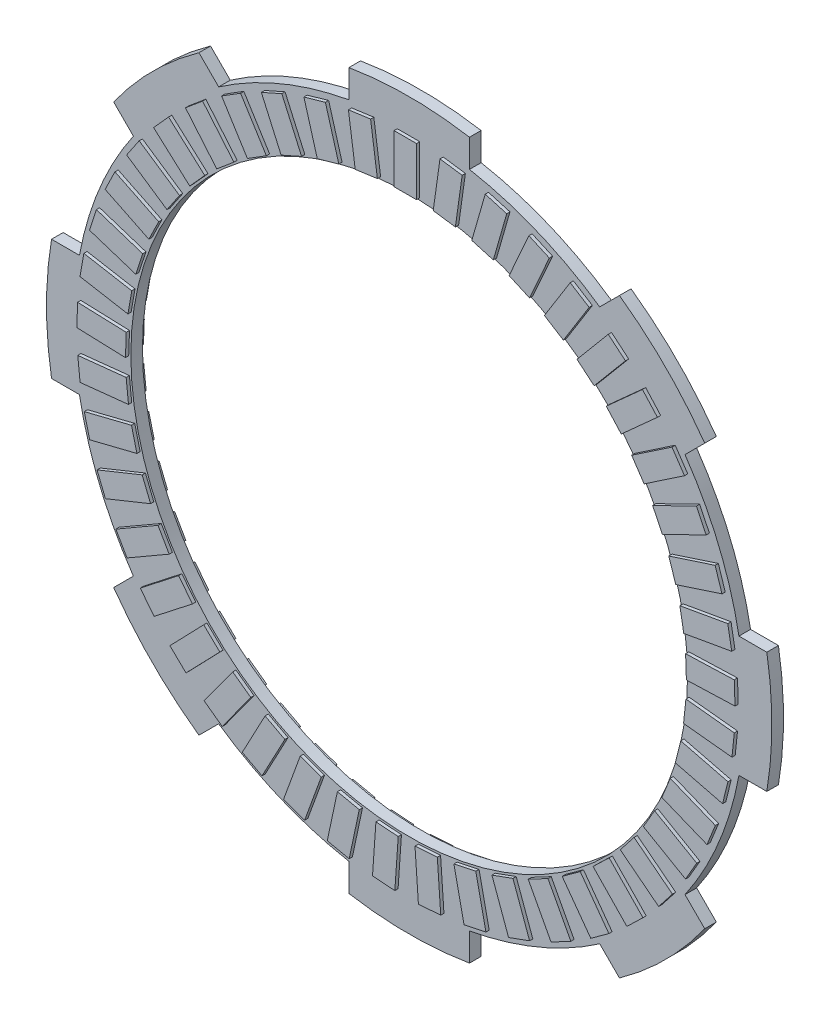
SolidWorks part; units mm, degrees
ref_plane "Front Plane" through (0, 0, 0) normal (0, 0, 1) x (1, 0, 0)
ref_plane "Top Plane" through (0, 0, 0) normal (0, 1, 0) x (1, 0, 0)
ref_plane "Right Plane" through (0, 0, 0) normal (1, 0, 0) x (0, 0, -1)
sketch "Sketch1" plane through (0, 0, 0) normal (0, 0, 1) x (1, 0, 0)
  line L0 (34.391, 48.3396) -> (31.1639, 45.1125)
  line L2 (9.8632, 58.4993) -> (9.8632, 53.9356)
  line L4 (-9.8632, 58.4993) -> (-9.8632, 53.9356)
  line L5 (48.3396, 34.391) -> (45.1125, 31.1639)
  line L6 (58.4993, 9.8632) -> (53.9356, 9.8632)
  line L7 (58.4993, -9.8632) -> (53.9356, -9.8632)
  line L8 (48.3396, -34.391) -> (45.1125, -31.1639)
  line L9 (34.391, -48.3396) -> (31.1639, -45.1125)
  line L10 (9.8632, -58.4993) -> (9.8632, -53.9356)
  line L11 (-9.8632, -58.4993) -> (-9.8632, -53.9356)
  line L12 (-34.391, -48.3396) -> (-31.1639, -45.1125)
  line L13 (-48.3396, -34.391) -> (-45.1125, -31.1639)
  line L14 (-58.4993, -9.8632) -> (-53.9356, -9.8632)
  line L15 (-58.4993, 9.8632) -> (-53.9356, 9.8632)
  line L16 (-48.3396, 34.391) -> (-45.1125, 31.1639)
  line L17 (-34.391, 48.3396) -> (-31.1639, 45.1125)
  circle A0 centre (0, 0) radius 45.53
  arc A1 (-9.8632, 53.9356) -> (-31.1639, 45.1125) centre (0, 0) ccw
  arc A2 (-34.391, 48.3396) -> (-48.3396, 34.391) centre (0, 0) ccw
  arc A3 (-9.8632, 53.9356) -> (-31.1639, 45.1125) centre (0, 0) ccw
  arc A4 (-9.8632, 53.9356) -> (-31.1639, 45.1125) centre (0, 0) ccw
  arc A5 (-9.8632, 53.9356) -> (-31.1639, 45.1125) centre (0, 0) ccw
  arc A6 (-9.8632, 53.9356) -> (-31.1639, 45.1125) centre (0, 0) ccw
  arc A7 (-9.8632, 53.9356) -> (-31.1639, 45.1125) centre (0, 0) ccw
  arc A8 (-9.8632, 53.9356) -> (-31.1639, 45.1125) centre (0, 0) ccw
  arc A9 (-9.8632, 53.9356) -> (-31.1639, 45.1125) centre (0, 0) ccw
  arc A10 (9.8632, 58.4993) -> (-9.8632, 58.4993) centre (0, 0) ccw
  arc A11 (48.3396, 34.391) -> (34.391, 48.3396) centre (0, 0) ccw
  arc A12 (31.1639, 45.1125) -> (9.8632, 53.9356) centre (0, 0) ccw
  arc A13 (31.1639, 45.1125) -> (9.8632, 53.9356) centre (0, 0) ccw
  arc A14 (31.1639, 45.1125) -> (9.8632, 53.9356) centre (0, 0) ccw
  arc A15 (31.1639, 45.1125) -> (9.8632, 53.9356) centre (0, 0) ccw
  arc A16 (31.1639, 45.1125) -> (9.8632, 53.9356) centre (0, 0) ccw
  arc A17 (31.1639, 45.1125) -> (9.8632, 53.9356) centre (0, 0) ccw
  arc A18 (31.1639, 45.1125) -> (9.8632, 53.9356) centre (0, 0) ccw
  arc A19 (31.1639, 45.1125) -> (9.8632, 53.9356) centre (0, 0) ccw
  arc A20 (53.9356, 9.8632) -> (45.1125, 31.1639) centre (0, 0) ccw
  arc A21 (53.9356, 9.8632) -> (45.1125, 31.1639) centre (0, 0) ccw
  arc A22 (53.9356, 9.8632) -> (45.1125, 31.1639) centre (0, 0) ccw
  arc A23 (53.9356, 9.8632) -> (45.1125, 31.1639) centre (0, 0) ccw
  arc A24 (53.9356, 9.8632) -> (45.1125, 31.1639) centre (0, 0) ccw
  arc A25 (53.9356, 9.8632) -> (45.1125, 31.1639) centre (0, 0) ccw
  arc A26 (53.9356, 9.8632) -> (45.1125, 31.1639) centre (0, 0) ccw
  arc A27 (53.9356, 9.8632) -> (45.1125, 31.1639) centre (0, 0) ccw
  arc A28 (58.4993, -9.8632) -> (58.4993, 9.8632) centre (0, 0) ccw
  arc A29 (45.1125, -31.1639) -> (53.9356, -9.8632) centre (0, 0) ccw
  arc A30 (45.1125, -31.1639) -> (53.9356, -9.8632) centre (0, 0) ccw
  arc A31 (45.1125, -31.1639) -> (53.9356, -9.8632) centre (0, 0) ccw
  arc A32 (45.1125, -31.1639) -> (53.9356, -9.8632) centre (0, 0) ccw
  arc A33 (45.1125, -31.1639) -> (53.9356, -9.8632) centre (0, 0) ccw
  arc A34 (45.1125, -31.1639) -> (53.9356, -9.8632) centre (0, 0) ccw
  arc A35 (45.1125, -31.1639) -> (53.9356, -9.8632) centre (0, 0) ccw
  arc A36 (45.1125, -31.1639) -> (53.9356, -9.8632) centre (0, 0) ccw
  arc A37 (34.391, -48.3396) -> (48.3396, -34.391) centre (0, 0) ccw
  arc A38 (9.8632, -53.9356) -> (31.1639, -45.1125) centre (0, 0) ccw
  arc A39 (9.8632, -53.9356) -> (31.1639, -45.1125) centre (0, 0) ccw
  arc A40 (9.8632, -53.9356) -> (31.1639, -45.1125) centre (0, 0) ccw
  arc A41 (9.8632, -53.9356) -> (31.1639, -45.1125) centre (0, 0) ccw
  arc A42 (9.8632, -53.9356) -> (31.1639, -45.1125) centre (0, 0) ccw
  arc A43 (9.8632, -53.9356) -> (31.1639, -45.1125) centre (0, 0) ccw
  arc A44 (9.8632, -53.9356) -> (31.1639, -45.1125) centre (0, 0) ccw
  arc A45 (9.8632, -53.9356) -> (31.1639, -45.1125) centre (0, 0) ccw
  arc A46 (-9.8632, -58.4993) -> (9.8632, -58.4993) centre (0, 0) ccw
  arc A47 (-31.1639, -45.1125) -> (-9.8632, -53.9356) centre (0, 0) ccw
  arc A48 (-31.1639, -45.1125) -> (-9.8632, -53.9356) centre (0, 0) ccw
  arc A49 (-31.1639, -45.1125) -> (-9.8632, -53.9356) centre (0, 0) ccw
  arc A50 (-31.1639, -45.1125) -> (-9.8632, -53.9356) centre (0, 0) ccw
  arc A51 (-31.1639, -45.1125) -> (-9.8632, -53.9356) centre (0, 0) ccw
  arc A52 (-31.1639, -45.1125) -> (-9.8632, -53.9356) centre (0, 0) ccw
  arc A53 (-31.1639, -45.1125) -> (-9.8632, -53.9356) centre (0, 0) ccw
  arc A54 (-31.1639, -45.1125) -> (-9.8632, -53.9356) centre (0, 0) ccw
  arc A55 (-48.3396, -34.391) -> (-34.391, -48.3396) centre (0, 0) ccw
  arc A56 (-53.9356, -9.8632) -> (-45.1125, -31.1639) centre (0, 0) ccw
  arc A57 (-53.9356, -9.8632) -> (-45.1125, -31.1639) centre (0, 0) ccw
  arc A58 (-53.9356, -9.8632) -> (-45.1125, -31.1639) centre (0, 0) ccw
  arc A59 (-53.9356, -9.8632) -> (-45.1125, -31.1639) centre (0, 0) ccw
  arc A60 (-53.9356, -9.8632) -> (-45.1125, -31.1639) centre (0, 0) ccw
  arc A61 (-53.9356, -9.8632) -> (-45.1125, -31.1639) centre (0, 0) ccw
  arc A62 (-53.9356, -9.8632) -> (-45.1125, -31.1639) centre (0, 0) ccw
  arc A63 (-53.9356, -9.8632) -> (-45.1125, -31.1639) centre (0, 0) ccw
  arc A64 (-58.4993, 9.8632) -> (-58.4993, -9.8632) centre (0, 0) ccw
  arc A65 (-45.1125, 31.1639) -> (-53.9356, 9.8632) centre (0, 0) ccw
  arc A66 (-45.1125, 31.1639) -> (-53.9356, 9.8632) centre (0, 0) ccw
  arc A67 (-45.1125, 31.1639) -> (-53.9356, 9.8632) centre (0, 0) ccw
  arc A68 (-45.1125, 31.1639) -> (-53.9356, 9.8632) centre (0, 0) ccw
  arc A69 (-45.1125, 31.1639) -> (-53.9356, 9.8632) centre (0, 0) ccw
  arc A70 (-45.1125, 31.1639) -> (-53.9356, 9.8632) centre (0, 0) ccw
  arc A71 (-45.1125, 31.1639) -> (-53.9356, 9.8632) centre (0, 0) ccw
  arc A72 (-45.1125, 31.1639) -> (-53.9356, 9.8632) centre (0, 0) ccw
  point P5 (0, 54.83)
  point P48 (0, 0)
  dimension "D1" = 109.66
  dimension "D2" = 91.06
  dimension "D3" = 118.65
  dimension "D4" = 8
extrude "Boss-Extrude1" add sketch "Sketch1" along normal blind 1.9 contours L16 A65 L15 A64 L14 A56 L13 A55 L12 A47 L11 A46 L10 A38 L9 A37 L8 A29 L7 A28 L6 A20 L5 A11 L0 A12 L2 A10 L4 A1 L17 A2 A0
sketch "Sketch2" plane through (0, 0, 1.9) normal (0, 0, 1) x (1, 0, 0)
  line L1 (1.7213, 45.8375) -> (-1.9387, 45.8375)
  line L2 (1.7213, 45.8375) -> (1.7213, 53.7975)
  line L3 (1.7213, 53.7975) -> (-1.9387, 53.7975)
  line L4 (-1.9387, 45.8375) -> (-1.9387, 53.7975)
  line L5 (1.7213, 45.8375) -> (-1.9387, 53.7975) construction
  line L6 (1.7213, 53.7975) -> (-1.9387, 45.8375) construction
  point P0 (-0.1087, 49.8175)
  dimension "D1" = 3.66
  dimension "D2" = 7.96
extrude "Boss-Extrude2" add sketch "Sketch2" along normal blind 0.53 contours L3 L4 L1 L2
pattern_circular "CirPattern1" count 45 over 360 about axis through (0, 0, 0) along (0, 0, 1) of "Boss-Extrude2"
sketch "Sketch5" plane through (0, 0, 0) normal (0, 0, -1) x (-1, 0, 0)
  line L1 (1.5084, 53.8234) -> (-2.1516, 53.8234)
  line L2 (1.5084, 53.8234) -> (1.5084, 45.8634)
  line L3 (1.5084, 45.8634) -> (-2.1516, 45.8634)
  line L4 (-2.1516, 53.8234) -> (-2.1516, 45.8634)
  line L5 (1.5084, 53.8234) -> (-2.1516, 45.8634) construction
  line L6 (1.5084, 45.8634) -> (-2.1516, 53.8234) construction
  point P0 (-0.3216, 49.8434)
  point P5 (0, 0)
  point P6 (0, 50.9792)
  point P7 (-0.371, 50.2385)
  point P8 (-0.3216, 49.8434)
  dimension "D1" = 3.66
  dimension "D2" = 7.96
extrude "Boss-Extrude3" add sketch "Sketch5" along normal blind 0.53
pattern_circular "CirPattern2" count 45 over 360 about axis through (0, 0, 0) along (0, 0, 1) of "Boss-Extrude3"
